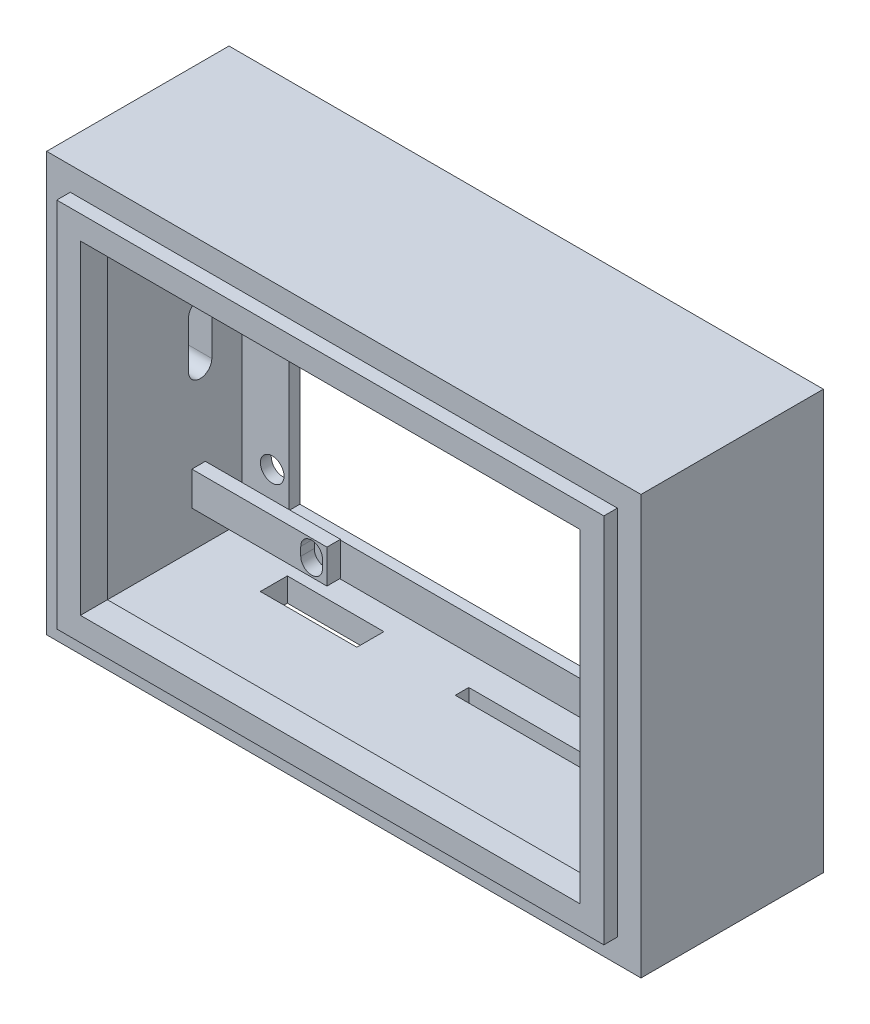
SolidWorks part; units mm, degrees
ref_plane "前视基准面" through (0, 0, 0) normal (0, 0, 1) x (1, 0, 0)
ref_plane "上视基准面" through (0, 0, 0) normal (0, 1, 0) x (1, 0, 0)
ref_plane "右视基准面" through (0, 0, 0) normal (1, 0, 0) x (0, 0, -1)
sketch "草图1" plane through (0, 0, 0) normal (0, 0, 1) x (1, 0, 0)
  line L1 (0, 0) -> (88, 0)
  line L2 (0, 0) -> (0, -62)
  line L3 (0, -62) -> (88, -62)
  line L4 (88, 0) -> (88, -62)
  dimension "D1" = 88
  dimension "D2" = 62
extrude "凸台-拉伸1" add sketch "草图1" along normal blind 2
sketch "草图2" plane through (0, 0, 2) normal (0, 0, 1) x (1, 0, 0)
  line L1 (0, 0) -> (3.5, 0) construction
  line L2 (0, 0) -> (0, -3.5) construction
  line L3 (0, -3.5) -> (3.5, -3.5) construction
  line L4 (3.5, 0) -> (3.5, -3.5) construction
  line L5 (88, -62) -> (84.5, -62) construction
  line L6 (88, -62) -> (88, -58.5) construction
  line L7 (88, -58.5) -> (84.5, -58.5) construction
  line L8 (84.5, -62) -> (84.5, -58.5) construction
  line L9 (3.5, -3.5) -> (84.5, -3.5)
  line L10 (3.5, -3.5) -> (3.5, -58.5)
  line L11 (3.5, -58.5) -> (84.5, -58.5)
  line L12 (84.5, -3.5) -> (84.5, -58.5)
  line L13 (3.5, -3.5) -> (7, -3.5) construction
  line L14 (3.5, -3.5) -> (3.5, -7) construction
  line L15 (3.5, -7) -> (7, -7) construction
  line L16 (7, -3.5) -> (7, -7) construction
  line L17 (84.5, -58.5) -> (81, -58.5) construction
  line L18 (84.5, -58.5) -> (84.5, -55) construction
  line L19 (84.5, -55) -> (81, -55) construction
  line L20 (81, -58.5) -> (81, -55) construction
  line L21 (7, -7) -> (81, -7)
  line L22 (7, -7) -> (7, -55)
  line L23 (7, -55) -> (81, -55)
  line L24 (81, -7) -> (81, -55)
  dimension "D1" = 3.5
  dimension "D2" = 3.5
  dimension "D3" = 3.5
  dimension "D4" = 3.5
  dimension "D5" = 3.5
  dimension "D6" = 3.5
  dimension "D7" = 3.5
  dimension "D8" = 3.5
extrude "凸台-拉伸2" add sketch "草图2" along normal blind 2
sketch "草图3" plane through (0, 0, 0) normal (0, 0, -1) x (-1, 0, 0)
  line L1 (-88, 0) -> (-84.5, 0) construction
  line L2 (-88, 0) -> (-88, -3.5) construction
  line L3 (-88, -3.5) -> (-84.5, -3.5) construction
  line L4 (-84.5, 0) -> (-84.5, -3.5) construction
  line L5 (0, -62) -> (-3.5, -62) construction
  line L6 (0, -62) -> (0, -58.5) construction
  line L7 (0, -58.5) -> (-3.5, -58.5) construction
  line L8 (-3.5, -62) -> (-3.5, -58.5) construction
  line L9 (-84.5, -3.5) -> (-3.5, -3.5)
  line L10 (-84.5, -3.5) -> (-84.5, -58.5)
  line L11 (-84.5, -58.5) -> (-3.5, -58.5)
  line L12 (-3.5, -3.5) -> (-3.5, -58.5)
  line L13 (-88, 0) -> (0, 0)
  line L14 (-88, 0) -> (-88, -62)
  line L15 (-88, -62) -> (0, -62)
  line L16 (0, 0) -> (0, -62)
  line M17 (0, -62) -> (0, 0)
  line M18 (0, 0) -> (-88, 0)
  line M19 (-88, 0) -> (-88, -62)
  line M20 (-88, -62) -> (0, -62)
  dimension "D1" = 3.5
  dimension "D2" = 3.5
  dimension "D3" = 3.5
  dimension "D4" = 3.5
extrude "凸台-拉伸3" add sketch "草图3" along normal blind 25 contours L9 L12 L11 L10 M20 M17 M18 M19
sketch "草图5" plane through (0, 0, 2) normal (0, 0, 1) x (1, 0, 0)
  line L1 (7, -7) -> (81, -7)
  line L2 (7, -7) -> (7, -55)
  line L3 (7, -55) -> (81, -55)
  line L4 (81, -7) -> (81, -55)
extrude "切除-拉伸1" cut sketch "草图5" against normal blind 20
sketch "草图6" plane through (0, 0, -25) normal (0, 0, -1) x (-1, 0, 0)
  line L0 (-3.5, -3.5) -> (-3.5, -58.5) construction
  line L1 (-84.5, -3.5) -> (-3.5, -3.5)
  line L2 (-84.5, -3.5) -> (-84.5, -8.5)
  line L3 (-84.5, -8.5) -> (-3.5, -8.5)
  line L4 (-3.5, -3.5) -> (-3.5, -8.5)
  line L5 (-3.5, -3.5) -> (-3.5, -58.5) construction
  line L6 (-84.5, -58.5) -> (-3.5, -58.5)
  line L7 (-84.5, -58.5) -> (-84.5, -53.5)
  line L8 (-84.5, -53.5) -> (-3.5, -53.5)
  line L9 (-3.5, -58.5) -> (-3.5, -53.5)
  line L11 (-3.5, -8.5) -> (-8, -8.5) construction
  line L12 (-84.5, -8.5) -> (-82.5, -8.5)
  line L13 (-84.5, -8.5) -> (-84.5, -53.5)
  line L14 (-84.5, -53.5) -> (-82.5, -53.5)
  line L15 (-82.5, -8.5) -> (-82.5, -53.5)
  line L16 (-3.5, -8.5) -> (-10.5, -8.5)
  line L17 (-3.5, -8.5) -> (-3.5, -53.5)
  line L18 (-3.5, -53.5) -> (-10.5, -53.5)
  line L19 (-10.5, -8.5) -> (-10.5, -53.5)
  line L20 (-3.5, -8.5) -> (-3.5, -12.5) construction
  line L21 (-3.5, -12.5) -> (-8, -12.5) construction
  line L22 (-8, -8.5) -> (-8, -12.5) construction
  line L23 (-3.5, -53.5) -> (-8, -53.5) construction
  line L24 (-3.5, -53.5) -> (-3.5, -49.5) construction
  line L25 (-3.5, -49.5) -> (-8, -49.5) construction
  line L26 (-8, -53.5) -> (-8, -49.5) construction
  circle A0 centre (-8, -49.5) radius 1.75
  circle A1 centre (-8, -12.5) radius 1.75
  line M17 (-84.5, -3.5) -> (-3.5, -3.5)
  line M18 (-3.5, -3.5) -> (-3.5, -58.5)
  line M19 (-3.5, -58.5) -> (-84.5, -58.5)
  line M20 (-84.5, -58.5) -> (-84.5, -3.5)
  dimension "D9" = 3.5
  dimension "D10" = 3.5
  dimension "D1" = 5
  dimension "D2" = 5
  dimension "D3" = 2
  dimension "D4" = 7
  dimension "D5" = 4.5
  dimension "D6" = 4
  dimension "D7" = 4.5
  dimension "D8" = 4
extrude "凸台-拉伸4" add sketch "草图6" against normal blind 1.6 contours L3 M20 M18 M17 | L3 L19 L8 A1 A0 M18 | L15 L3 L8 M20 | L8 M20 M19 M18
sketch "草图7" plane through (0, -62, 0) normal (0, -1, 0) x (1, 0, 0)
  line L1 (88, -25) -> (75.5, -25) construction
  line L2 (88, -25) -> (88, -19) construction
  line L3 (88, -19) -> (75.5, -19) construction
  line L4 (75.5, -25) -> (75.5, -19) construction
  line L5 (75.5, -19) -> (41.5, -19)
  line L6 (75.5, -19) -> (75.5, -17)
  line L7 (75.5, -17) -> (41.5, -17)
  line L8 (41.5, -19) -> (41.5, -17)
  line L9 (13.762, -15.8751) -> (28.0577, -15.8751)
  line L10 (13.762, -15.8751) -> (13.762, -19.8751)
  line L11 (13.762, -19.8751) -> (28.0577, -19.8751)
  line L12 (28.0577, -15.8751) -> (28.0577, -19.8751)
  dimension "D1" = 12.5
  dimension "D2" = 34
  dimension "D3" = 2
  dimension "D4" = 6
  dimension "D5" = 4
sketch "草图8" plane through (3.5, 0, 0) normal (1, 0, 0) x (0, 0, -1)
  line L1 (16, -48) -> (18, -48)
  line L2 (16, -48) -> (16, -53)
  line L3 (16, -53) -> (18, -53)
  line L4 (18, -48) -> (18, -53)
  line L5 (25, -62) -> (18, -62) construction
  line L6 (25, -62) -> (25, -53) construction
  line L7 (25, -53) -> (18, -53) construction
  line L8 (18, -62) -> (18, -53) construction
  dimension "D1" = 7
  dimension "D2" = 9
  dimension "D3" = 2
  dimension "D4" = 5
extrude "凸台-拉伸5" add sketch "草图8" along normal blind 20 contours L4 L1 L2 L3 | L6 L5 L8 L7
sketch "草图10" plane through (0, 0, -18) normal (0, 0, -1) x (-1, 0, 0)
  line L0 (-21.2286, -49.845) -> (-21.2286, -51.1198) construction
  line L1 (-19.6234, -49.845) -> (-19.6234, -51.1198)
  line L2 (-22.8339, -49.845) -> (-22.8339, -51.1198)
  arc A0 (-19.6234, -49.845) -> (-22.8339, -49.845) centre (-21.2286, -49.845) ccw
  arc A1 (-22.8339, -51.1198) -> (-19.6234, -51.1198) centre (-21.2286, -51.1198) ccw
  point P2 (-21.2286, -50.4824)
extrude "切除-拉伸2" cut sketch "草图10" against normal blind 17
extrude "切除-拉伸3" cut sketch "草图7" against normal blind 5
sketch "草图11" plane through (0, 0, 0) normal (-1, 0, 0) x (0, 0, 1)
  line L0 (-17.2307, -28.3937) -> (-17.2307, -35.2873) construction
  line L1 (-15.5073, -28.3937) -> (-15.5073, -35.2873)
  line L2 (-18.9541, -28.3937) -> (-18.9541, -35.2873)
  arc A0 (-15.5073, -28.3937) -> (-18.9541, -28.3937) centre (-17.2307, -28.3937) ccw
  arc A1 (-18.9541, -35.2873) -> (-15.5073, -35.2873) centre (-17.2307, -35.2873) ccw
  point P2 (-17.2307, -31.8405)
extrude "切除-拉伸4" cut sketch "草图11" against normal blind 5
